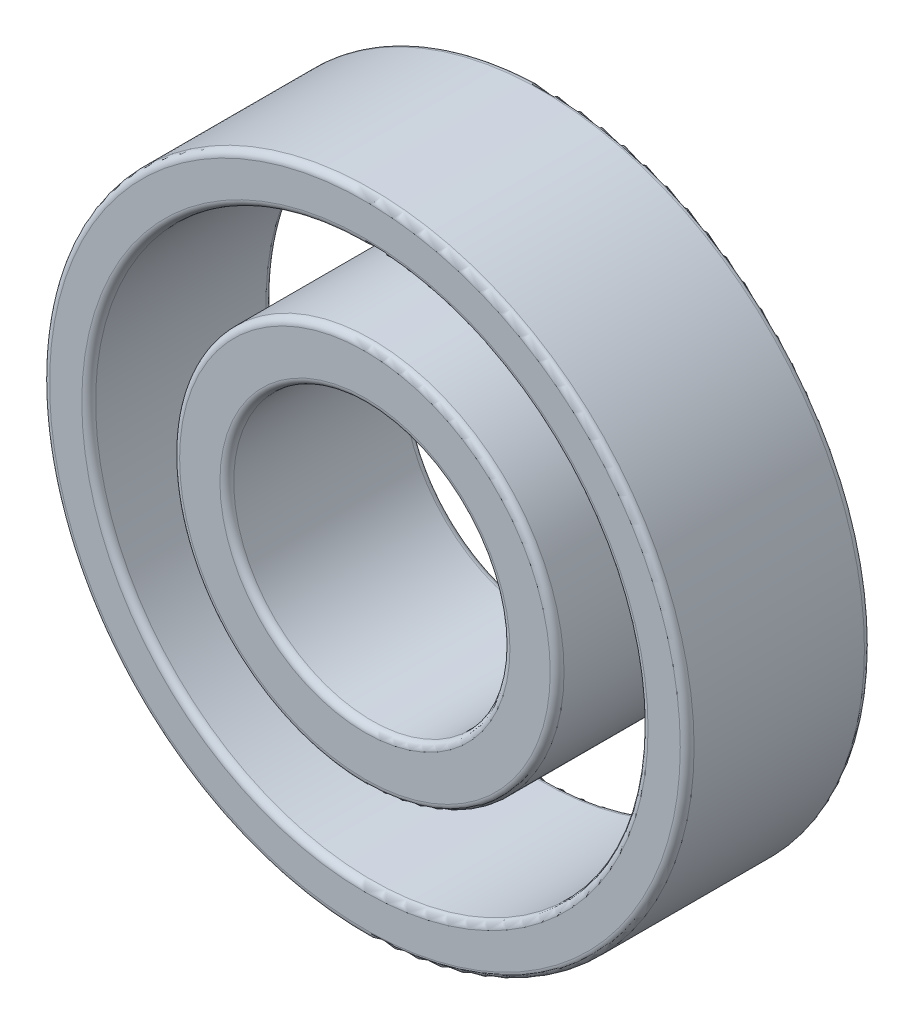
SolidWorks part; units mm, degrees
ref_plane "Front Plane" through (0, 0, 0) normal (0, 0, 1) x (1, 0, 0)
ref_plane "Top Plane" through (0, 0, 0) normal (0, 1, 0) x (1, 0, 0)
ref_plane "Right Plane" through (0, 0, 0) normal (1, 0, 0) x (0, 0, -1)
sketch "Sketch1" plane through (0, 0, 0) normal (0, 0, 1) x (1, 0, 0)
  circle A0 centre (0, 0) radius 14
  circle A1 centre (0, 0) radius 6
  circle A2 centre (0, 0) radius 8.35
  circle A3 centre (0, 0) radius 12
  dimension "D1" = 28
  dimension "D2" = 12
  dimension "D3" = 16.7
  dimension "D4" = 24
extrude "Boss-Extrude1" add sketch "Sketch1" along normal blind 8 contours A0 | A3 | A2 | A1
ref_plane "Middle Plane" through (0, 0, 4) normal (0, 0, 1) x (1, 0, 0)
sketch "Sketch2" plane through (0, 0, 4) normal (0, 0, 1) x (1, 0, 0)
  circle A0 centre (0, 0) radius 10.175
  dimension "D1" = 20.35
fillet "Fillet1" radius 0.3 4 edges at (12, 0, 0) (14, 0, 0) (12, 0, 8) (14, 0, 8)
fillet "Fillet2" radius 0.3 4 edges at (6, 0, 8) (8.35, 0, 8) (6, 0, 0) (8.35, 0, 0)
